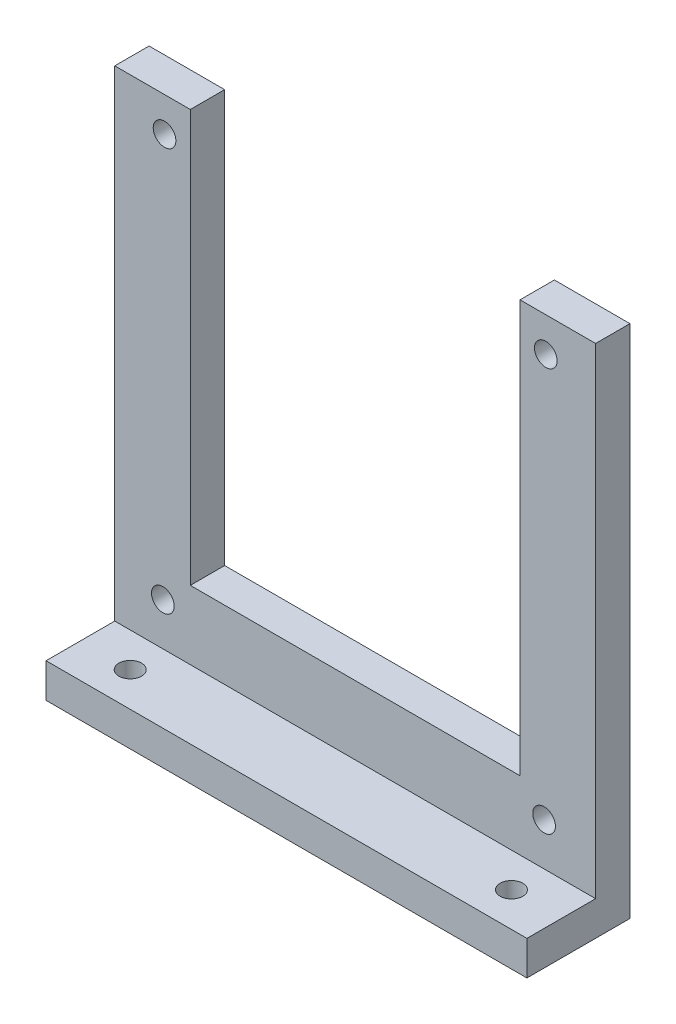
SolidWorks part; units mm, degrees
ref_plane "Ebene vorne" through (0, 0, 0) normal (0, 0, 1) x (1, 0, 0)
ref_plane "Ebene oben" through (0, 0, 0) normal (0, 1, 0) x (1, 0, 0)
ref_plane "Ebene rechts" through (0, 0, 0) normal (1, 0, 0) x (0, 0, -1)
sketch "Skizze1" plane through (0, 0, 0) normal (0, 0, 1) x (1, 0, 0)
  line L1 (-35, -7.5) -> (35, -7.5)
  line L2 (-35, -7.5) -> (-35, 7.5)
  line L3 (-35, 7.5) -> (35, 7.5)
  line L4 (35, -7.5) -> (35, 7.5)
  line L5 (-35, -7.5) -> (35, 7.5) construction
  line L6 (-35, 7.5) -> (35, -7.5) construction
  line L11 (35, -7.5) -> (24, -7.5)
  line L12 (35, -7.5) -> (35, 67.5)
  line L13 (35, 67.5) -> (24, 67.5)
  line L14 (24, -7.5) -> (24, 67.5)
  line L15 (-35, -7.5) -> (-24, -7.5)
  line L16 (-35, -7.5) -> (-35, 67.5)
  line L17 (-35, 67.5) -> (-24, 67.5)
  line L18 (-24, -7.5) -> (-24, 67.5)
  point P0 (0, 0)
  dimension "D1" = 70
  dimension "D2" = 15
  dimension "D3" = 75
  dimension "D4" = 75
  dimension "D5" = 48
  dimension "D6" = 24
extrude "Aufsatz-Linear austragen1" add sketch "Skizze1" along normal blind 5 contours L3 L18 L17 L16 | L1 L18 L3 L2 | L18 L1 L14 L3 | L14 L1 L4 L3 | L14 L3 L12 L13
sketch "Skizze2" plane through (0, 0, 5) normal (0, 0, 1) x (1, 0, 0)
  line L3 (-35, 67.5) -> (-24, 67.5) construction
  line L4 (35, 67.5) -> (24, 67.5) construction
  line L5 (0, -2.75) -> (0, 2.75) construction
  line L6 (-35, -7.5) -> (-35, 67.5) construction
  circle A0 centre (-27.9978, 3.7005) radius 1.65
  circle A1 centre (27.5022, 3.7005) radius 1.65
  circle A2 centre (27.75, 62.5) radius 1.65
  circle A3 centre (-27.75, 62.5) radius 1.65
  dimension "D5" = 3.3
  dimension "D1" = 55.5
  dimension "D2" = 27.5022
  dimension "D3" = 58.8
  dimension "D4" = 58.8
  dimension "D6" = 5
  dimension "D7" = 5
extrude "Schnitt-Linear austragen1" cut sketch "Skizze2" against normal blind 5
sketch "Skizze6" plane through (0, 0, 5) normal (0, 0, 1) x (1, 0, 0)
  line L0 (35, -7.5) -> (35, 67.5) construction
  line L1 (-35, -7.5) -> (35, -7.5)
  line L2 (-35, -7.5) -> (-35, -2.5)
  line L3 (-35, -2.5) -> (35, -2.5)
  line L4 (35, -7.5) -> (35, -2.5)
  dimension "D1" = 5
extrude "Aufsatz-Linear austragen3" add sketch "Skizze6" along normal blind 10
sketch "Skizze7" plane through (0, -2.5, 0) normal (0, 1, 0) x (1, 0, 0)
  line L0 (-35, -15) -> (-35, -5) construction
  line L1 (35, -15) -> (35, -5) construction
  line L2 (35, -15) -> (-35, -15) construction
  circle A0 centre (-27.75, -10) radius 1.65
  circle A1 centre (27.75, -10) radius 1.65
  dimension "D3" = 3.3
  dimension "D4" = 5
  dimension "D1" = 7.25
  dimension "D2" = 7.25
  dimension "D5" = 5
extrude "Schnitt-Linear austragen2" cut sketch "Skizze7" against normal blind 10
